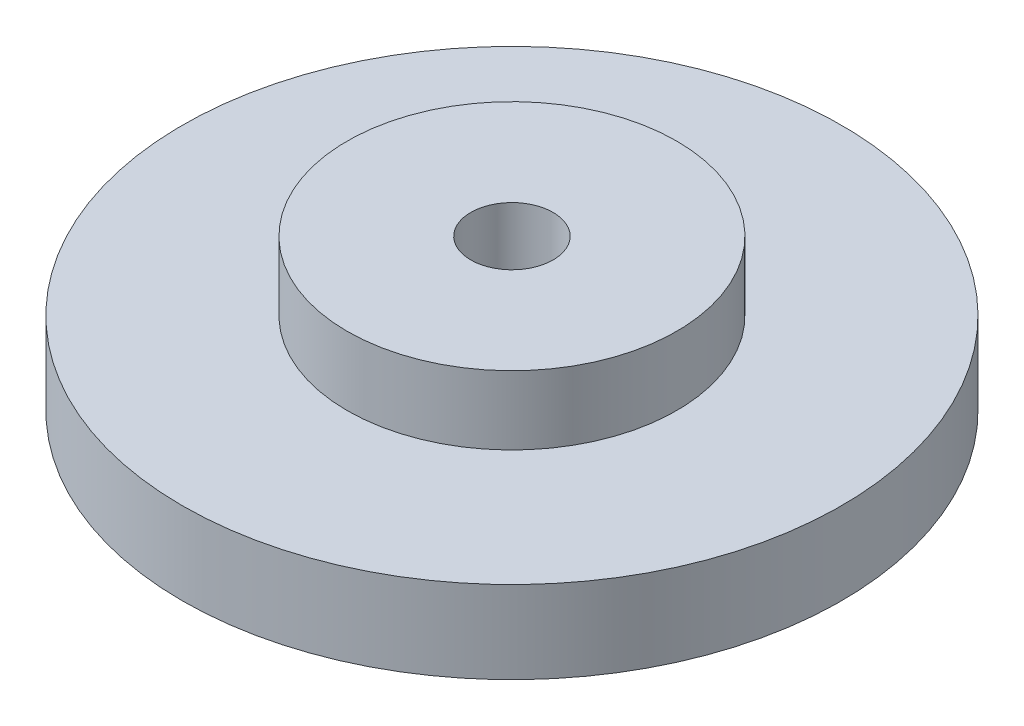
SolidWorks part; units mm, degrees
ref_plane "Front Plane" through (0, 0, 0) normal (0, 0, 1) x (1, 0, 0)
ref_plane "Top Plane" through (0, 0, 0) normal (0, 1, 0) x (1, 0, 0)
ref_plane "Right Plane" through (0, 0, 0) normal (1, 0, 0) x (0, 0, -1)
sketch "Sketch1" plane through (0, 0, 0) normal (0, 1, 0) x (1, 0, 0)
  circle A0 centre (0, 0) radius 48
  dimension "D1" = 96
extrude "Boss-Extrude1" add sketch "Sketch1" along normal blind 12
sketch "Sketch2" plane through (0, 12, 0) normal (0, 1, 0) x (1, 0, 0)
  circle A0 centre (0, 0) radius 24
  dimension "D1" = 48
extrude "Boss-Extrude2" add sketch "Sketch2" along normal blind 10
sketch "Sketch3" plane through (0, 22, 0) normal (0, 1, 0) x (1, 0, 0)
  circle A0 centre (0, 0) radius 6
  dimension "D1" = 12
extrude "Cut-Extrude1" cut sketch "Sketch3" against normal blind 34
sketch "Sketch4" plane through (0, 0, 0) normal (0, -1, 0) x (1, 0, 0)
  circle A0 centre (0, 36) radius 4
  circle A1 centre (31.1769, 18) radius 4
  circle A2 centre (31.1769, -18) radius 4
  circle A3 centre (0, -36) radius 4
  circle A4 centre (-31.1769, -18) radius 4
  circle A5 centre (-31.1769, 18) radius 4
  point P15 (0, 0)
  dimension "D1" = 8
  dimension "D2" = 36
  dimension "D3" = 6
extrude "Cut-Extrude2" cut sketch "Sketch4" against normal blind 10
